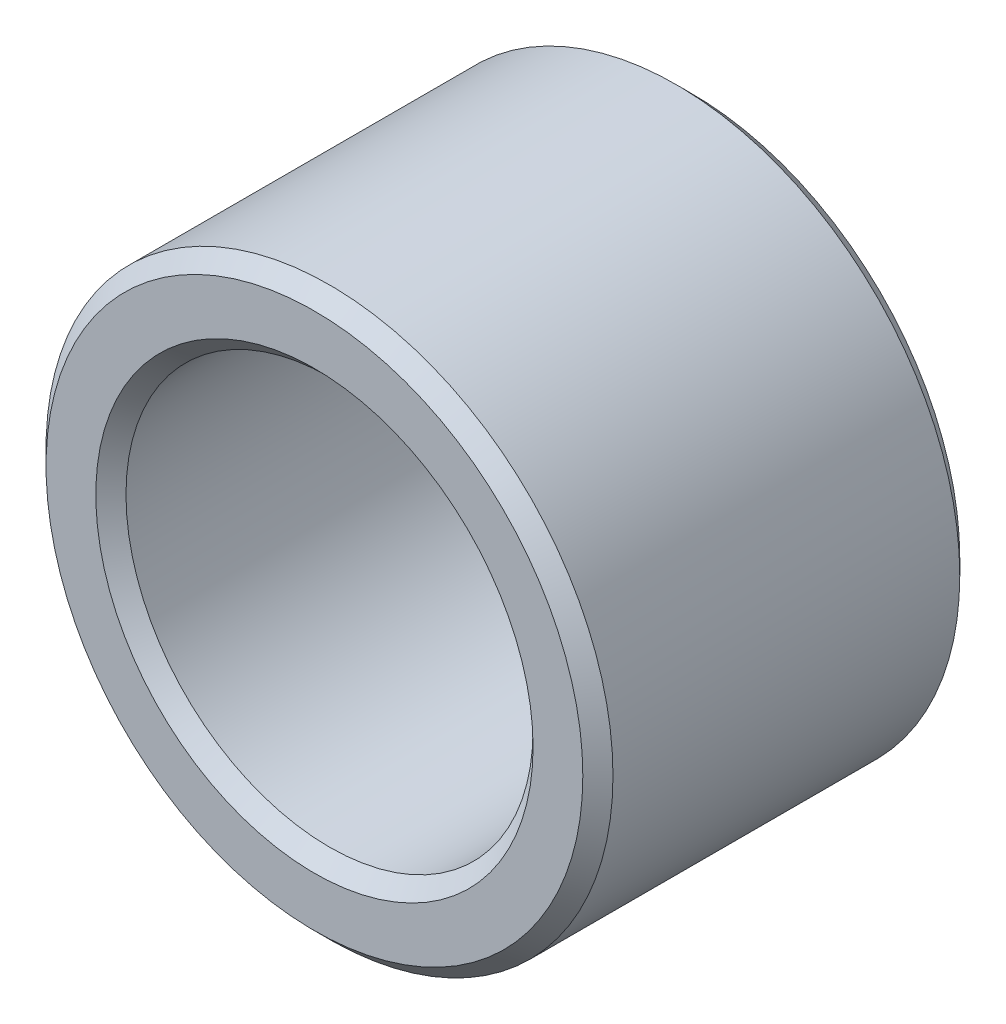
SolidWorks part; units mm, degrees
material "Onyx"
ref_plane "Front Plane" through (0, 0, 0) normal (0, 0, 1) x (1, 0, 0)
ref_plane "Top Plane" through (0, 0, 0) normal (0, 1, 0) x (1, 0, 0)
ref_plane "Right Plane" through (0, 0, 0) normal (1, 0, 0) x (0, 0, -1)
sketch "Sketch1" plane through (0, 0, 0) normal (0, 0, 1) x (1, 0, 0)
  circle A0 centre (0, 0) radius 4.7752
  circle A1 centre (0, 0) radius 3.429
  dimension "D1" = 9.5504
  dimension "ID" = 6.858
extrude "Extrude1" add sketch "Sketch1" along normal mid plane 6.35
sketch "Sketch2" plane through (0, 0, 0) normal (1, 0, 0) x (0, 0, -1)
  line L0 (-3.175, -3.429) -> (3.175, -3.429) construction
  line L3 (3.175, 3.429) -> (-3.175, 3.429) construction
  line L5 (-3.175, -3.429) -> (3.175, -3.429)
  line L6 (3.175, 3.429) -> (-3.175, 3.429)
sketch "Sketch4" plane through (0, 0, 3.175) normal (0, 0, 1) x (1, 0, 0)
  line L0 (0, 0) -> (-2.4247, 2.4247)
  line L1 (0, -55) -> (0, 55) construction
  circle A0 centre (0, 0) radius 3.429 construction
  dimension "D1" = 45
chamfer "Chamfer1" distance 0.254 angle 45 4 edges at (3.429, 0, -3.175) (4.7752, 0, -3.175) (3.429, 0, 3.175) (4.7752, 0, 3.175)
